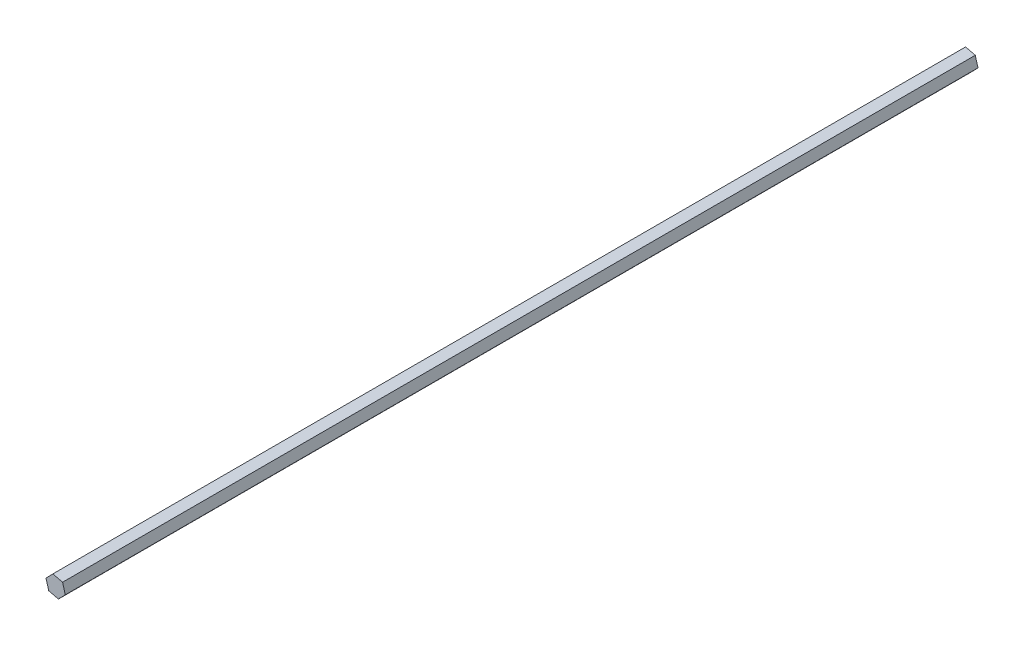
SolidWorks part; units mm, degrees
ref_plane "Front Plane" through (0, 0, 0) normal (0, 0, 1) x (1, 0, 0)
ref_plane "Top Plane" through (0, 0, 0) normal (0, 1, 0) x (1, 0, 0)
ref_plane "Right Plane" through (0, 0, 0) normal (1, 0, 0) x (0, 0, -1)
sketch "Sketch1" plane through (0, 0, 0) normal (0, 0, 1) x (1, 0, 0)
  line L1 (-7.1134, 1.7784) -> (-5.0968, -5.2712)
  line L2 (-5.0968, -5.2712) -> (2.0166, -7.0496)
  line L3 (2.0166, -7.0496) -> (7.1134, -1.7784)
  line L4 (7.1134, -1.7784) -> (5.0968, 5.2712)
  line L5 (5.0968, 5.2712) -> (-2.0166, 7.0496)
  line L6 (-2.0166, 7.0496) -> (-7.1134, 1.7784)
  circle A0 centre (0, 0) radius 6.35 construction
  dimension "D1" = 12.7
extrude "Boss-Extrude1" add sketch "Sketch1" along normal blind 673.1
